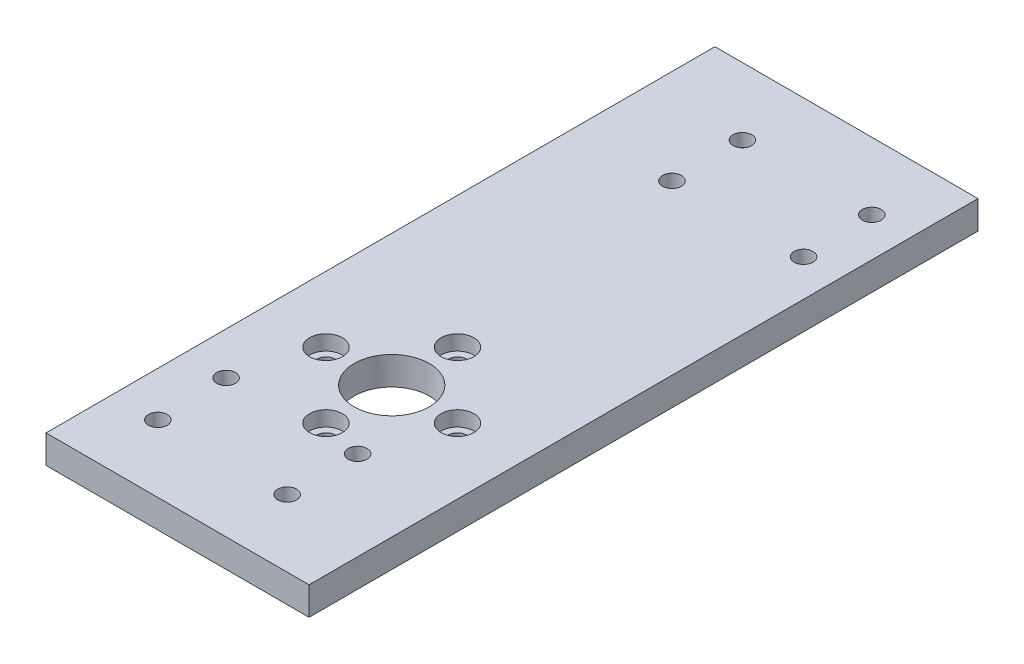
SolidWorks part; units mm, degrees
material "Custom Plastic"
ref_plane "Front Plane" through (0, 0, 0) normal (0, 0, 1) x (1, 0, 0)
ref_plane "Top Plane" through (0, 0, 0) normal (0, 1, 0) x (1, 0, 0)
ref_plane "Right Plane" through (0, 0, 0) normal (1, 0, 0) x (0, 0, -1)
sketch "Sketch1" plane through (0, 0, 0) normal (0, 1, 0) x (1, 0, 0)
  line L1 (-14, -35.6) -> (14, -35.6)
  line L2 (-14, -35.6) -> (-14, 35.6)
  line L3 (-14, 35.6) -> (14, 35.6)
  line L4 (14, -35.6) -> (14, 35.6)
  line L5 (-14, -35.6) -> (14, 35.6) construction
  line L6 (-14, 35.6) -> (14, -35.6) construction
  point P0 (0, 0)
  dimension "D1" = 71.2
  dimension "D2" = 28
extrude "Boss-Extrude1" add sketch "Sketch1" along normal blind 3
sketch "Sketch4" plane through (0, 3, 0) normal (0, 1, 0) x (1, 0, 0)
  line L0 (0, -2.5883) -> (0, -23.7562) construction
  line L1 (14, -35.6) -> (14, 35.6) construction
  circle A0 centre (7, -12.8) radius 1
  circle A1 centre (0, -19.8) radius 1
  circle A2 centre (-7, -12.8) radius 1
  circle A4 centre (0, -5.8) radius 1
  circle A9 centre (0, -12.8) radius 7 construction
  point P18 (0, -12.8)
  dimension "D1" = 2
  dimension "D2" = 14
  dimension "D4" = 14
  dimension "D3" = 4
extrude "Cut-Extrude2" cut sketch "Sketch4" against normal blind 10
sketch "Sketch5" plane through (0, 3, 0) normal (0, 1, 0) x (1, 0, 0)
  line L2 (-14, -35.6) -> (14, -35.6) construction
  line L3 (14, -35.6) -> (14, 35.6) construction
  circle A0 centre (0, -12.8) radius 4
  dimension "D1" = 8
  dimension "D2" = 22.8
  dimension "D3" = 14
extrude "Cut-Extrude3" cut sketch "Sketch5" against normal blind 10
sketch "Sketch7" plane through (0, 3, 0) normal (0, 1, 0) x (1, 0, 0)
  circle A0 centre (-9.4812, -20.9482) radius 1 construction
  circle A1 centre (-9.2488, -28.4482) radius 1 construction
  circle A2 centre (4.5188, -28.4482) radius 1 construction
  circle A3 centre (4.5188, -20.9482) radius 1 construction
  circle A4 centre (-9.4812, -20.9482) radius 1
  circle A5 centre (-9.2488, -28.4482) radius 1
  circle A6 centre (4.5188, -28.4482) radius 1
  circle A7 centre (4.5188, -20.9482) radius 1
extrude "Cut-Extrude6" cut sketch "Sketch7" against normal blind 10
sketch "Sketch8" plane through (0, 3, 0) normal (0, 1, 0) x (1, 0, 0)
  circle A0 centre (-3.9188, 28.4482) radius 1 construction
  circle A1 centre (9.8488, 28.4482) radius 1 construction
  circle A2 centre (10.0812, 20.9482) radius 1 construction
  circle A3 centre (-3.9188, 20.9482) radius 1 construction
  circle A4 centre (-3.9188, 28.4482) radius 1
  circle A5 centre (9.8488, 28.4482) radius 1
  circle A6 centre (10.0812, 20.9482) radius 1
  circle A7 centre (-3.9188, 20.9482) radius 1
extrude "Cut-Extrude7" cut sketch "Sketch8" against normal blind 10
sketch "Sketch9" plane through (0, 3, 0) normal (0, 1, 0) x (1, 0, 0)
  circle A1 centre (-9.2488, -28.4482) radius 1.75
  circle A2 centre (-9.2488, -28.4482) radius 1.75
  circle A3 centre (10.0812, 20.9482) radius 1.75
  circle A4 centre (10.0812, 20.9482) radius 1.75
  circle A5 centre (9.8488, 28.4482) radius 1.75
  circle A6 centre (9.8488, 28.4482) radius 1.75
  circle A7 centre (-3.9188, 20.9482) radius 1.75
  circle A8 centre (-3.9188, 20.9482) radius 1.75
  circle A9 centre (-3.9188, 28.4482) radius 1.75
  circle A10 centre (-3.9188, 28.4482) radius 1.75
  circle A11 centre (4.5188, -20.9482) radius 1.75
  circle A12 centre (4.5188, -20.9482) radius 1.75
  circle A13 centre (4.5188, -28.4482) radius 1.75
  circle A14 centre (4.5188, -28.4482) radius 1.75
  circle A15 centre (-9.4812, -20.9482) radius 1.75
  circle A16 centre (-9.4812, -20.9482) radius 1.75
  dimension "D1" = 0
  dimension "D2" = 0
  dimension "D3" = 0
  dimension "D4" = 0
  dimension "D5" = 0
  dimension "D6" = 0
  dimension "D7" = 0
  dimension "D8" = 0
sketch "Sketch10" plane through (0, 3, 0) normal (0, 1, 0) x (1, 0, 0)
  circle A0 centre (0, -19.8) radius 1.75
  circle A1 centre (-7, -12.8) radius 1.75
  circle A2 centre (0, -5.8) radius 1.75
  circle A3 centre (7, -12.8) radius 1.75
  dimension "D1" = 3.5
  dimension "D2" = 3.5
  dimension "D3" = 3.5
  dimension "D4" = 3.5
extrude "Cut-Extrude9" cut sketch "Sketch10" against normal blind 1.6
sketch "Sketch11" plane through (0, 0, 0) normal (0, -1, 0) x (1, 0, 0)
  circle A1 centre (-3.9188, -20.9482) radius 1.75
  circle A2 centre (-3.9188, -20.9482) radius 1.75
  circle A3 centre (9.8488, -28.4482) radius 1.75
  circle A4 centre (9.8488, -28.4482) radius 1.75
  circle A5 centre (10.0812, -20.9482) radius 1.75
  circle A6 centre (10.0812, -20.9482) radius 1.75
  circle A7 centre (-9.2488, 28.4482) radius 1.75
  circle A8 centre (-9.2488, 28.4482) radius 1.75
  circle A9 centre (-9.4812, 20.9482) radius 1.75
  circle A10 centre (-9.4812, 20.9482) radius 1.75
  circle A11 centre (4.5188, 28.4482) radius 1.75
  circle A12 centre (4.5188, 28.4482) radius 1.75
  circle A13 centre (4.5188, 20.9482) radius 1.75
  circle A14 centre (4.5188, 20.9482) radius 1.75
  circle A15 centre (-3.9188, -28.4482) radius 1.75
  circle A16 centre (-3.9188, -28.4482) radius 1.75
  dimension "D1" = 0
  dimension "D2" = 0
  dimension "D3" = 0
  dimension "D4" = 0
  dimension "D5" = 0
  dimension "D6" = 0
  dimension "D7" = 0
  dimension "D8" = 0
extrude "Cut-Extrude10" cut sketch "Sketch11" against normal blind 1.6
